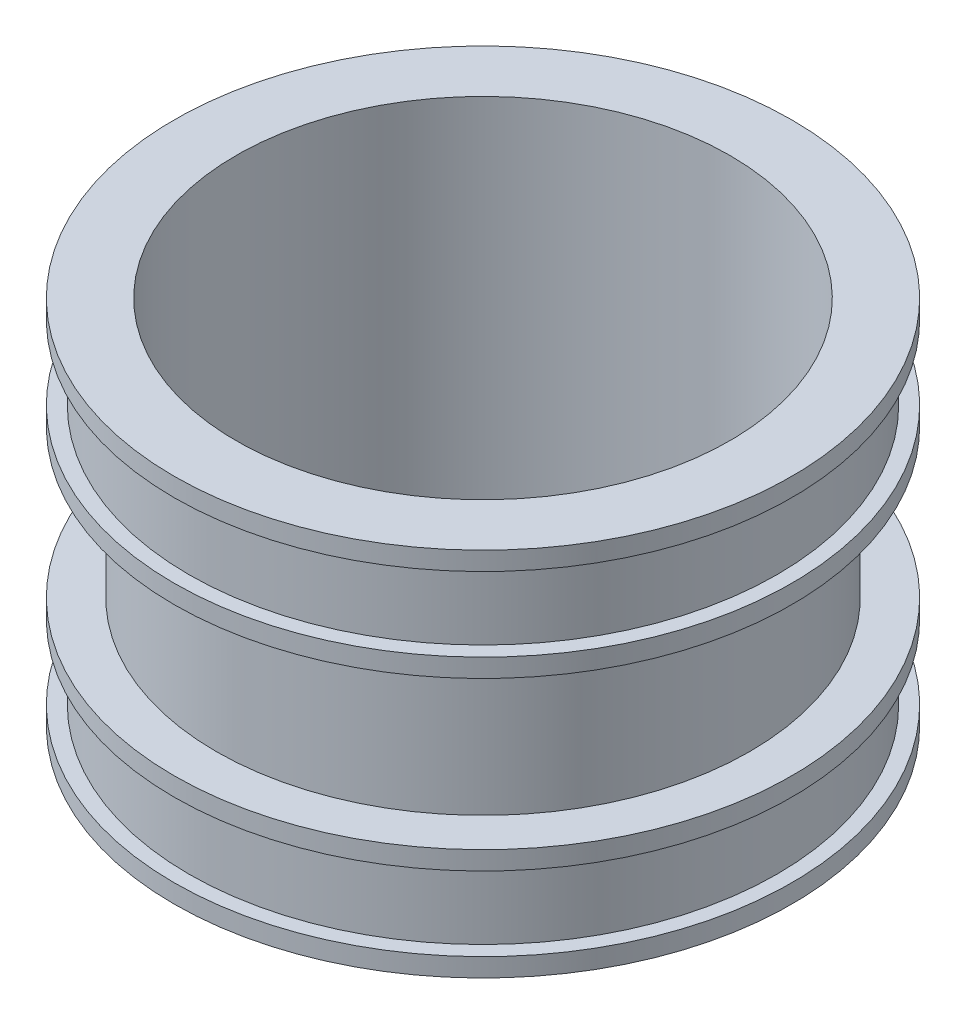
SolidWorks part; units mm, degrees
material "AISI 1020"
ref_plane "Plano frontal" through (0, 0, 0) normal (0, 0, 1) x (1, 0, 0)
ref_plane "Plano superior" through (0, 0, 0) normal (0, 1, 0) x (1, 0, 0)
ref_plane "Plano direito" through (0, 0, 0) normal (1, 0, 0) x (0, 0, -1)
sketch "Esboço1" plane through (0, 0, 0) normal (0, 0, 1) x (1, 0, 0)
  line L0 (0, 0) -> (0, 327.1613) construction
  line L1 (0, 0) -> (502.3995, 0) construction
  line L2 (100, 150) -> (125, 150)
  line L3 (125, 150) -> (125, 142.5)
  line L4 (125, 105) -> (108, 105)
  line L5 (108, 105) -> (108, 45)
  line L6 (108, 45) -> (125, 45)
  line L7 (125, 45) -> (125, 37.5)
  line L8 (125, 0) -> (100, 0)
  line L9 (100, 0) -> (100, 150)
  line L10 (125, 142.5) -> (119, 142.5)
  line L11 (119, 142.5) -> (119, 112.5)
  line L12 (119, 112.5) -> (125, 112.5)
  line L13 (100, 75) -> (125, 75) construction
  line L14 (125, 112.5) -> (125, 105)
  line L15 (119, 37.5) -> (125, 37.5)
  line L16 (119, 7.5) -> (119, 37.5)
  line L17 (125, 7.5) -> (119, 7.5)
  line L18 (125, 7.5) -> (125, 0)
  point P22 (108, 75)
  dimension "D1" = 200
  dimension "D2" = 6
  dimension "D3" = 30
  dimension "D4" = 45
  dimension "250" = 250
  dimension "D6" = 8
  dimension "D7" = 150
revolve "Revolução1" add sketch "Esboço1" angle 360 about L0
